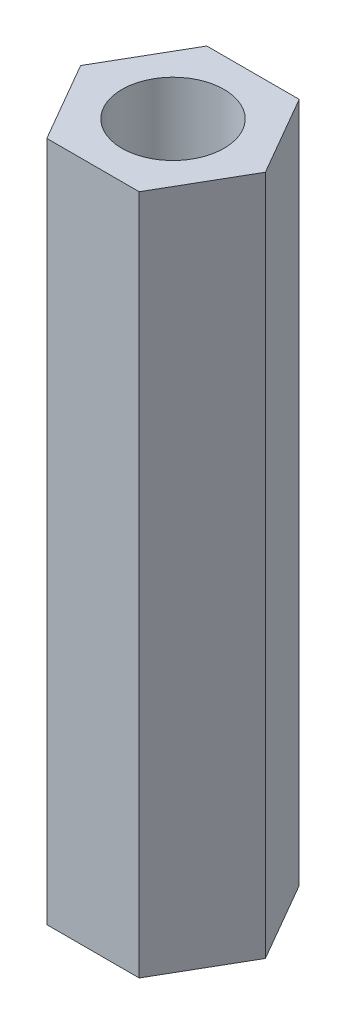
SolidWorks part; units mm, degrees
ref_plane "Front Plane" through (0, 0, 0) normal (0, 0, 1) x (1, 0, 0)
ref_plane "Top Plane" through (0, 0, 0) normal (0, 1, 0) x (1, 0, 0)
ref_plane "Right Plane" through (0, 0, 0) normal (1, 0, 0) x (0, 0, -1)
sketch "Sketch2" plane through (0, 0, 0) normal (0, 1, 0) x (1, 0, 0)
  line L1 (2.7135, 0) -> (1.3568, 2.35)
  line L2 (1.3568, 2.35) -> (-1.3568, 2.35)
  line L3 (-1.3568, 2.35) -> (-2.7135, 0)
  line L4 (-2.7135, 0) -> (-1.3568, -2.35)
  line L5 (-1.3568, -2.35) -> (1.3568, -2.35)
  line L6 (1.3568, -2.35) -> (2.7135, 0)
  circle A0 centre (0, 0) radius 2.35 construction
  circle A1 centre (0, 0) radius 1.5
  dimension "D1" = 4.7
  dimension "D3" = 3
  dimension "D2" = 2.35
extrude "Boss-Extrude1" add sketch "Sketch2" along normal blind 20
